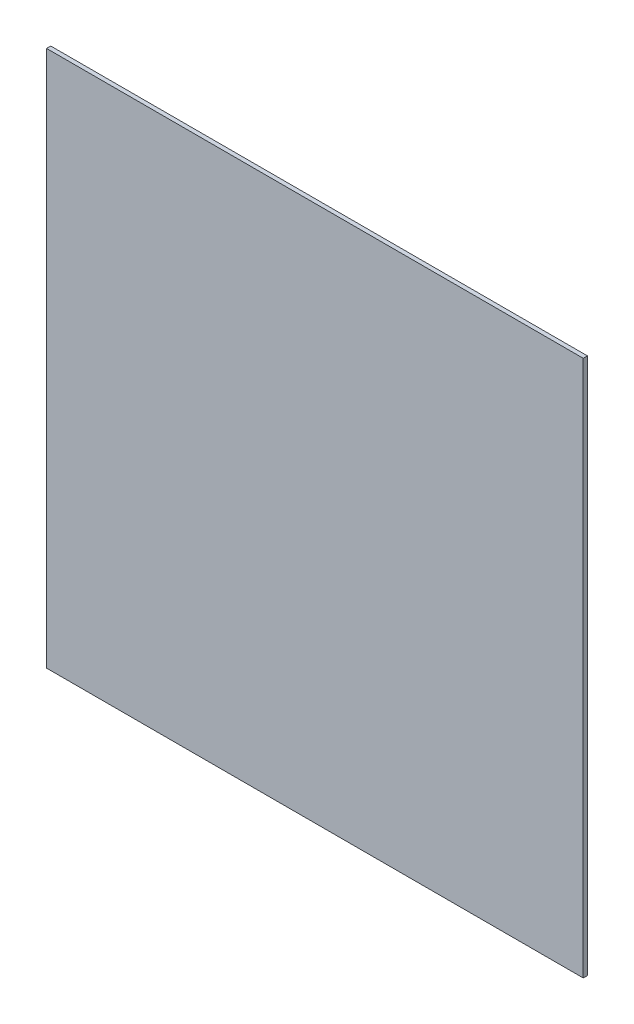
SolidWorks part; units mm, degrees
ref_plane "Front Plane" through (0, 0, 0) normal (0, 0, 1) x (1, 0, 0)
ref_plane "Top Plane" through (0, 0, 0) normal (0, 1, 0) x (1, 0, 0)
ref_plane "Right Plane" through (0, 0, 0) normal (1, 0, 0) x (0, 0, -1)
sketch "Sketch1" plane through (0, 0, 0) normal (0, 0, 1) x (1, 0, 0)
  line L1 (0, 0) -> (101.6, 0)
  line L2 (0, 0) -> (0, -101.6)
  line L3 (0, -101.6) -> (101.6, -101.6)
  line L4 (101.6, 0) -> (101.6, -101.6)
  dimension "D1" = 101.6
  dimension "D2" = 101.6
extrude "Plaque" add sketch "Sketch1" along normal blind 0.7937
